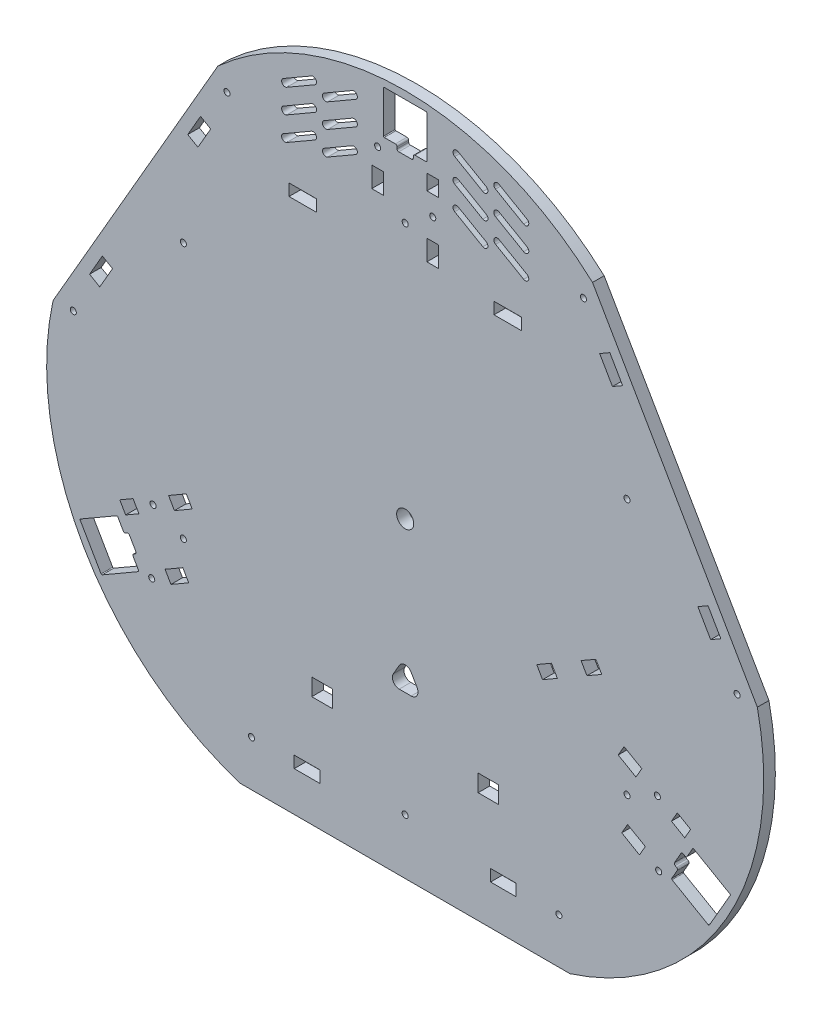
SolidWorks part; units mm, degrees
ref_plane "Front Plane" through (0, 0, 0) normal (0, 0, 1) x (1, 0, 0)
ref_plane "Top Plane" through (0, 0, 0) normal (0, 1, 0) x (1, 0, 0)
ref_plane "Right Plane" through (0, 0, 0) normal (1, 0, 0) x (0, 0, -1)
sketch "Sketch1" plane through (0, 0, 0) normal (0, 0, 1) x (1, 0, 0)
  line L0 (-96.5063, -182.3938) -> (96.5063, -182.3938)
  line L1 (206.2108, 7.62) -> (109.7045, 174.7738)
  line L2 (-109.7045, 174.7738) -> (-206.2108, 7.62)
  line L3 (0, 0) -> (-157.9577, 91.1969) construction
  line L4 (0, 0) -> (157.9577, 91.1969) construction
  line L5 (0, 0) -> (0, -182.3938) construction
  arc A0 (-206.2108, 7.62) -> (-96.5063, -182.3938) centre (-46.9534, -27.1085) ccw
  arc A1 (96.5063, -182.3938) -> (206.2108, 7.62) centre (46.9534, -27.1085) ccw
  arc A2 (109.7045, 174.7738) -> (-109.7045, 174.7738) centre (0, 54.2171) ccw
  circle A3 centre (0, 0) radius 5
  dimension "D1" = 163
  dimension "D6" = 10
  dimension "D2" = 193.0125
  dimension "D3" = 60
  dimension "D4" = 182.3938
  dimension "D5" = 120
extrude "Boss-Extrude1" add sketch "Sketch1" along normal blind 6.8
sketch "Sketch2" plane through (0, 0, 6.8) normal (0, 0, 1) x (1, 0, 0)
  line L4 (0, 0) -> (-157.9577, 91.1969) construction
  line L5 (-109.7045, 174.7738) -> (-206.2108, 7.62) construction
  line L6 (-104.3494, 164.1692) -> (-116.8494, 142.5186) construction
  line L7 (-178.8702, 28.2152) -> (-184.8285, 31.6552)
  line L8 (-184.8285, 31.6552) -> (-177.3285, 44.6456)
  line L9 (-171.3702, 41.2056) -> (-178.8702, 28.2152)
  line L10 (-177.3285, 44.6456) -> (-171.3702, 41.2056)
  line L11 (0, 0) -> (0, 309.3666) construction
  line L12 (-113.8702, 140.7986) -> (-121.3702, 127.8082)
  line L13 (-127.3285, 131.2482) -> (-119.8285, 144.2386)
  line L14 (-177.3285, 44.6456) -> (-184.8285, 31.6552)
  line L15 (-178.8702, 28.2152) -> (-171.3702, 41.2056)
  line L16 (127.3285, 131.2482) -> (121.3702, 127.8082)
  line L17 (119.8285, 144.2386) -> (127.3285, 131.2482)
  line L18 (113.8702, 140.7986) -> (119.8285, 144.2386)
  line L19 (121.3702, 127.8082) -> (113.8702, 140.7986)
  line L20 (-121.3702, 127.8082) -> (-113.8702, 140.7986)
  line L21 (-113.8702, 140.7986) -> (-119.8285, 144.2386)
  line L22 (-119.8285, 144.2386) -> (-127.3285, 131.2482)
  line L23 (-127.3285, 131.2482) -> (-121.3702, 127.8082)
  line L24 (178.8702, 28.2152) -> (171.3702, 41.2056)
  line L25 (177.3285, 44.6456) -> (184.8285, 31.6552)
  line L26 (127.3285, 131.2482) -> (119.8285, 144.2386)
  line L27 (113.8702, 140.7986) -> (121.3702, 127.8082)
  line L28 (-65, -159.1438) -> (-50, -159.1438)
  line L29 (-50, -159.1438) -> (-50, -152.2638)
  line L30 (-50, -152.2638) -> (-65, -152.2638)
  line L31 (-65, -152.2638) -> (-65, -159.1438)
  line L32 (177.3285, 44.6456) -> (171.3702, 41.2056)
  line L33 (171.3702, 41.2056) -> (178.8702, 28.2152)
  line L34 (184.8285, 31.6552) -> (177.3285, 44.6456)
  line L35 (178.8702, 28.2152) -> (184.8285, 31.6552)
  line L36 (90, -155.7038) -> (65, -155.7038) construction
  line L37 (65, -152.2638) -> (65, -159.1438)
  line L38 (50, -152.2638) -> (65, -152.2638)
  line L39 (50, -159.1438) -> (50, -152.2638)
  line L40 (0, 0) -> (0, -243.079) construction
  line L41 (-96.5063, -182.3938) -> (96.5063, -182.3938) construction
  line L42 (-90, -155.7038) -> (-65, -155.7038) construction
  line L43 (65, -159.1438) -> (50, -159.1438)
  circle A4 centre (-194.3494, 8.2846) radius 1.775
  circle A5 centre (-104.3494, 164.1692) radius 1.775
  circle A6 centre (-90, -155.7038) radius 1.775
  circle A7 centre (90, -155.7038) radius 1.775
  circle A8 centre (104.3494, 164.1692) radius 1.775
  circle A9 centre (194.3494, 8.2846) radius 1.775
  point P11 (-181.8494, 29.9352)
  point P44 (181.8494, 29.9352)
  dimension "D6" = 3.55
  dimension "D1" = 50
  dimension "D2" = 15
  dimension "D3" = 6.88
  dimension "D4" = 25
  dimension "D5" = 6.5
  dimension "D7" = 50
  dimension "D8" = 15
  dimension "D9" = 6.88
  dimension "D10" = 23.25
  dimension "D11" = 25
extrude "Cut-Extrude1" cut sketch "Sketch2" against normal blind 6.8 contours L10 L8 L7 L9 | A4 | L13 L23 L12 L21 | A5 | A8 | L19 L16 L17 L18 | L24 L35 L25 L32 | A9 | L43 L37 L38 L39 | A7 | L30 L31 L28 L29 | A6
sketch "Sketch3" plane through (0, 0, 6.8) normal (0, 0, 1) x (1, 0, 0)
  line L0 (0, 0) -> (-188.1155, -108.6085) construction
  line L1 (-190.5536, -95.3515) -> (-177.8536, -117.3485)
  line L2 (-177.8536, -117.3485) -> (-155.8566, -104.6485)
  line L3 (-155.8566, -104.6485) -> (-159.8316, -97.7636)
  line L4 (-168.5566, -82.6515) -> (-190.5536, -95.3515)
  line L5 (-164.5816, -89.5364) -> (-161.9835, -88.0364)
  line L6 (-161.9835, -88.0364) -> (-157.2335, -96.2636)
  line L7 (-157.2335, -96.2636) -> (-159.8316, -97.7636)
  line L8 (-164.5816, -89.5364) -> (-168.5566, -82.6515)
  line L9 (-167.1468, -73.8932) -> (-159.3526, -69.3932)
  line L10 (-159.3526, -69.3932) -> (-155.9126, -75.3515)
  line L11 (-155.9126, -75.3515) -> (-163.7068, -79.8515)
  line L12 (-163.7068, -79.8515) -> (-167.1468, -73.8932)
  line L13 (-128.1757, -51.3932) -> (-138.568, -57.3932)
  line L14 (-138.568, -57.3932) -> (-135.128, -63.3515)
  line L15 (-135.128, -63.3515) -> (-124.7357, -57.3515)
  line L16 (-124.7357, -57.3515) -> (-128.1757, -51.3932)
  line L17 (-140.6145, -95.8485) -> (-137.1745, -101.8068)
  line L18 (-137.1745, -101.8068) -> (-126.7822, -95.8068)
  line L19 (-126.7822, -95.8068) -> (-130.2222, -89.8485)
  line L20 (-130.2222, -89.8485) -> (-140.6145, -95.8485)
  line L21 (-136.848, -60.3723) -> (-147.6579, -66.6134) construction
  line L22 (-148.4208, -104.3277) -> (-138.8945, -98.8277) construction
  arc A0 (-206.2108, 7.62) -> (-96.5063, -182.3938) centre (-46.9534, -27.1085) ccw construction
  circle A1 centre (-173.2051, -100) radius 12.7 construction
  circle A2 centre (-147.6579, -66.6134) radius 1.775
  circle A3 centre (-148.4208, -104.3277) radius 1.775
  dimension "D13" = 3.55
  dimension "D1" = 12.7
  dimension "D2" = 25.4
  dimension "D3" = 9.5
  dimension "D4" = 12.7
  dimension "D5" = 3
  dimension "D6" = 200
  dimension "D7" = 24
  dimension "D8" = 9
  dimension "D9" = 12
  dimension "D10" = 6.88
  dimension "D11" = 5.6
  dimension "D12" = 3
  dimension "D14" = 11
  dimension "D15" = 12.4822
extrude "Cut-Extrude2" cut sketch "Sketch3" against normal blind 6.8
fillet "Fillet1" radius 0.5 4 edges at (-155.8566, -104.6485, 3.4) (-177.8536, -117.3485, 3.4) (-190.5536, -95.3515, 3.4) (-168.5566, -82.6515, 3.4)
fillet "Fillet2" radius 1 4 edges at (-157.2335, -96.2636, 3.4) (-159.8316, -97.7636, 3.4) (-161.9835, -88.0364, 3.4) (-164.5816, -89.5364, 3.4)
mirror "Mirror1" about plane through (0, 0, 0) normal (1, 0, 0) of "Fillet1", "Fillet2", "Cut-Extrude2"
pattern_circular "CirPattern1" count 3 over 360 about axis through (0, 0, 6.8) along (0, 0, 1) skipping 1 of "Cut-Extrude2", "Fillet1", "Fillet2"
sketch "Sketch4" plane through (0, 0, 6.8) normal (0, 0, 1) x (1, 0, 0)
  circle A0 centre (0, 150) radius 1.775
  dimension "D2" = 3.55
  dimension "D1" = 150
extrude "Cut-Extrude3" cut sketch "Sketch4" against normal blind 6.8
pattern_circular "CirPattern2" count 6 over 360 about axis through (0, 0, 0) along (0, 0, 1) of "Cut-Extrude3"
sketch "Sketch5" plane through (0, 0, 6.8) normal (0, 0, 1) x (1, 0, 0)
  line L0 (-30, 200) -> (-46.4545, 190.5) construction
  line L1 (-29, 198.2679) -> (-45.4545, 188.7679)
  line L2 (-31, 201.7321) -> (-47.4545, 192.2321)
  line L3 (-12.7, 212.2) -> (-12.7, 187.8) construction
  line L4 (-53.9186, 195.4282) -> (-70.3731, 185.9282) construction
  line L5 (-52.9186, 193.6962) -> (-69.3731, 184.1962)
  line L6 (-54.9186, 197.1603) -> (-71.3731, 187.6603)
  line L7 (-52.1865, 196.4282) -> (-48.1865, 189.5) construction
  arc A0 (-29, 198.2679) -> (-31, 201.7321) centre (-30, 200) ccw
  arc A1 (-47.4545, 192.2321) -> (-45.4545, 188.7679) centre (-46.4545, 190.5) ccw
  arc A2 (-52.9186, 193.6962) -> (-54.9186, 197.1603) centre (-53.9186, 195.4282) ccw
  arc A3 (-71.3731, 187.6603) -> (-69.3731, 184.1962) centre (-70.3731, 185.9282) ccw
  point P2 (-38.2272, 195.25)
  point P12 (-62.1458, 190.6782)
  dimension "D3" = 2
  dimension "D1" = 30
  dimension "D2" = 19
  dimension "D4" = 200
  dimension "D5" = 60
  dimension "D6" = 4
extrude "Cut-Extrude4" cut sketch "Sketch5" against normal blind 6.8
pattern_linear "LPattern1" count 3 spacing 14 along (0, -1, 0) of "Cut-Extrude4"
mirror "Mirror2" about plane through (0, 0, 0) normal (1, 0, 0) of "LPattern1", "Cut-Extrude4"
sketch "Sketch6" plane through (0, 0, 6.8) normal (0, 0, 1) x (1, 0, 0)
  line L1 (52, 129.5) -> (68, 129.5)
  line L2 (52, 129.5) -> (52, 136.38)
  line L3 (52, 136.38) -> (68, 136.38)
  line L4 (68, 129.5) -> (68, 136.38)
  line L5 (52, 129.5) -> (68, 136.38) construction
  line L6 (52, 136.38) -> (68, 129.5) construction
  line L7 (-68, 129.5) -> (-52, 129.5)
  line L8 (-68, 129.5) -> (-68, 136.38)
  line L9 (-68, 136.38) -> (-52, 136.38)
  line L10 (-52, 129.5) -> (-52, 136.38)
  line L11 (-68, 129.5) -> (-52, 136.38) construction
  line L12 (-68, 136.38) -> (-52, 129.5) construction
  point P0 (60, 132.94)
  point P5 (-60, 132.94)
  dimension "D1" = 16
  dimension "D2" = 6.88
  dimension "D3" = 104
  dimension "D4" = 129.5
  dimension "D5" = 52
extrude "Cut-Extrude5" cut sketch "Sketch6" against normal blind 6.8
sketch "Sketch7" plane through (0, 0, 6.8) normal (0, 0, 1) x (1, 0, 0)
  line L0 (0, 0) -> (0, -216.7489) construction
  line L1 (-54.7, -107.5138) -> (-42.7, -107.5138)
  line L2 (-54.7, -107.5138) -> (-54.7, -117.5138)
  line L3 (-54.7, -117.5138) -> (-42.7, -117.5138)
  line L4 (-42.7, -107.5138) -> (-42.7, -117.5138)
  line L5 (-54.7, -107.5138) -> (-42.7, -117.5138) construction
  line L6 (-54.7, -117.5138) -> (-42.7, -107.5138) construction
  line L7 (54.7, -117.5138) -> (42.7, -117.5138)
  line L8 (54.7, -117.5138) -> (54.7, -107.5138)
  line L9 (54.7, -107.5138) -> (42.7, -107.5138)
  line L10 (42.7, -117.5138) -> (42.7, -107.5138)
  line L11 (54.7, -117.5138) -> (42.7, -107.5138) construction
  line L12 (54.7, -107.5138) -> (42.7, -117.5138) construction
  line L14 (-50, -152.2638) -> (-65, -152.2638) construction
  point P0 (-48.7, -112.5138)
  point P5 (48.7, -112.5138)
  dimension "D1" = 85.4
  dimension "D2" = 12
  dimension "D3" = 10
  dimension "D4" = 42.7
  dimension "D5" = 34.75
extrude "Cut-Extrude6" cut sketch "Sketch7" against normal blind 6.8
sketch "Sketch8" plane through (0, 0, 6.8) normal (0, 0, 1) x (1, 0, 0)
  line L0 (-3.4641, -76) -> (-6.9641, -82.0622)
  line L1 (-3.5, -88.0622) -> (3.5, -88.0622)
  line L2 (6.9641, -82.0622) -> (3.4641, -76)
  arc A0 (3.4641, -76) -> (-3.4641, -76) centre (0, -78) ccw
  arc A3 (3.5, -88.0622) -> (6.9641, -82.0622) centre (3.5, -84.0622) ccw
  arc A4 (-6.9641, -82.0622) -> (-3.5, -88.0622) centre (-3.5, -84.0622) ccw
  dimension "D2" = 4
  dimension "D4" = 60
  dimension "D1" = 7
  dimension "D3" = 78
  dimension "D5" = 60
extrude "Cut-Extrude8" cut sketch "Sketch8" against normal blind 6.8
sketch "Sketch9" plane through (0, 0, 6.8) normal (0, 0, 1) x (1, 0, 0)
  line L0 (-108.1756, -128.2) -> (-100.8244, -128.2)
  line L1 (-100.8244, -146.8) -> (-108.1756, -146.8)
  arc A0 (-100.8244, -146.8) -> (-100.8244, -128.2) centre (-104.5, -137.5) ccw
  circle A1 centre (0, 0) radius 5 construction
  circle A2 centre (0, 0) radius 5 construction
  arc A3 (-108.1756, -128.2) -> (-108.1756, -146.8) centre (-104.5, -137.5) ccw
  dimension "D1" = 20
  dimension "D5" = 104.5
  dimension "D2" = 18.6
  dimension "D3" = 9.3
  dimension "D4" = 137.5
extrude "Cut-Extrude9" [suppressed] cut sketch "Sketch9" against normal blind 6.8
sketch "Sketch10" plane through (0, 0, 6.8) normal (0, 0, 1) x (1, 0, 0)
  line L4 (111.6482, -15.3528) -> (115.0882, -21.311)
  line L5 (106.428, -26.311) -> (102.988, -20.3528)
  line L6 (85.6674, -30.3528) -> (89.1074, -36.311)
  line L7 (80.4472, -41.311) -> (77.0072, -35.3528)
  line L8 (115.0882, -21.311) -> (106.428, -26.311)
  line L9 (89.1074, -36.311) -> (80.4472, -41.311)
  line L10 (77.0072, -35.3528) -> (85.6674, -30.3528)
  line L11 (111.6482, -15.3528) -> (102.988, -20.3528)
extrude "Cut-Extrude10" cut sketch "Sketch10" against normal through all
